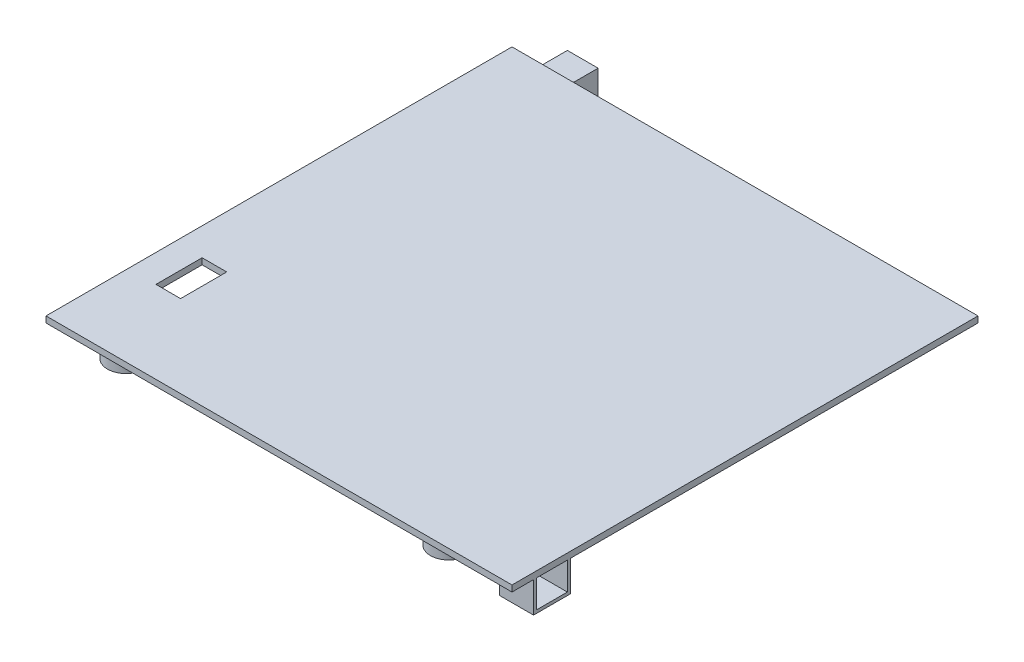
SolidWorks part; units mm, degrees
ref_plane "Front Plane" through (0, 0, 0) normal (0, 0, 1) x (1, 0, 0)
ref_plane "Top Plane" through (0, 0, 0) normal (0, 1, 0) x (1, 0, 0)
ref_plane "Right Plane" through (0, 0, 0) normal (1, 0, 0) x (0, 0, -1)
sketch "Sketch1" plane through (0, 0, 0) normal (0, 1, 0) x (1, 0, 0)
  line L1 (0, 0) -> (151.5, 0)
  line L2 (0, 0) -> (0, 151.5)
  line L3 (0, 151.5) -> (151.5, 151.5)
  line L4 (151.5, 0) -> (151.5, 151.5)
  dimension "D1" = 151.5
  dimension "D2" = 151.5
extrude "Boss-Extrude1" add sketch "Sketch1" along normal blind 2
sketch "Sketch8" plane through (0, 0, 0) normal (0, -1, 0) x (-1, 0, 0)
  circle A0 centre (-13, 13) radius 6
extrude "Boss-Extrude3" add sketch "Sketch8" along normal blind 10
sketch "Sketch9" plane through (0, 0, 0) normal (0, 1, 0) x (1, 0, 0)
  circle A0 centre (13, 13) radius 5
extrude "Cut-Extrude5" cut sketch "Sketch9" against normal blind 10
pattern_linear "LPattern3" count 2 spacing 105 along (1, 0, 0) count 2 spacing 105 along (0, 0, -1) of "Cut-Extrude5", "Boss-Extrude3"
sketch "Sketch10" plane through (0, 0, 0) normal (0, 1, 0) x (1, 0, 0)
  line L1 (8, 161.5) -> (18, 161.5)
  line L2 (8, 161.5) -> (8, 141.5)
  line L3 (8, 141.5) -> (18, 141.5)
  line L4 (18, 161.5) -> (18, 141.5)
  line L5 (8, 161.5) -> (18, 141.5) construction
  line L6 (8, 141.5) -> (18, 161.5) construction
  point P0 (13, 151.5)
  dimension "D1" = 10
  dimension "D2" = 20
extrude "Boss-Extrude4" add sketch "Sketch10" against normal blind 9
sketch "Sketch11" plane through (0, 0, 0) normal (0, -1, 0) x (-1, 0, 0)
  line L1 (-140.5, 7) -> (-151.5, 7)
  line L2 (-140.5, 7) -> (-140.5, 19)
  line L3 (-140.5, 19) -> (-151.5, 19)
  line L4 (-151.5, 7) -> (-151.5, 19)
  line L5 (-140.5, 7) -> (-151.5, 19) construction
  line L6 (-140.5, 19) -> (-151.5, 7) construction
  point P0 (-146, 13)
  dimension "D1" = 12
  dimension "D2" = 11
extrude "Boss-Extrude5" add sketch "Sketch11" along normal blind 10
sketch "Sketch13" plane through (151.5, 0, 0) normal (1, 0, 0) x (0, 0, -1)
  line L1 (8, 0) -> (18, 0)
  line L2 (8, 0) -> (8, -9)
  line L3 (8, -9) -> (18, -9)
  line L4 (18, 0) -> (18, -9)
  line L5 (8, 0) -> (18, -9) construction
  line L6 (8, -9) -> (18, 0) construction
  point P0 (13, -4.5)
  dimension "D1" = 10
  dimension "D2" = 9
extrude "Cut-Extrude6" cut sketch "Sketch13" against normal blind 10
sketch "Sketch15" plane through (0, 0, 0) normal (0, 1, 0) x (1, 0, 0)
  line L1 (9, 26.75) -> (17, 26.75)
  line L2 (9, 26.75) -> (9, 41.75)
  line L3 (9, 41.75) -> (17, 41.75)
  line L4 (17, 26.75) -> (17, 41.75)
  line L5 (9, 26.75) -> (17, 41.75) construction
  line L6 (9, 41.75) -> (17, 26.75) construction
  point P0 (13, 34.25)
  dimension "D1" = 8
  dimension "D2" = 15
extrude "Cut-Extrude7" cut sketch "Sketch15" along normal blind 2
